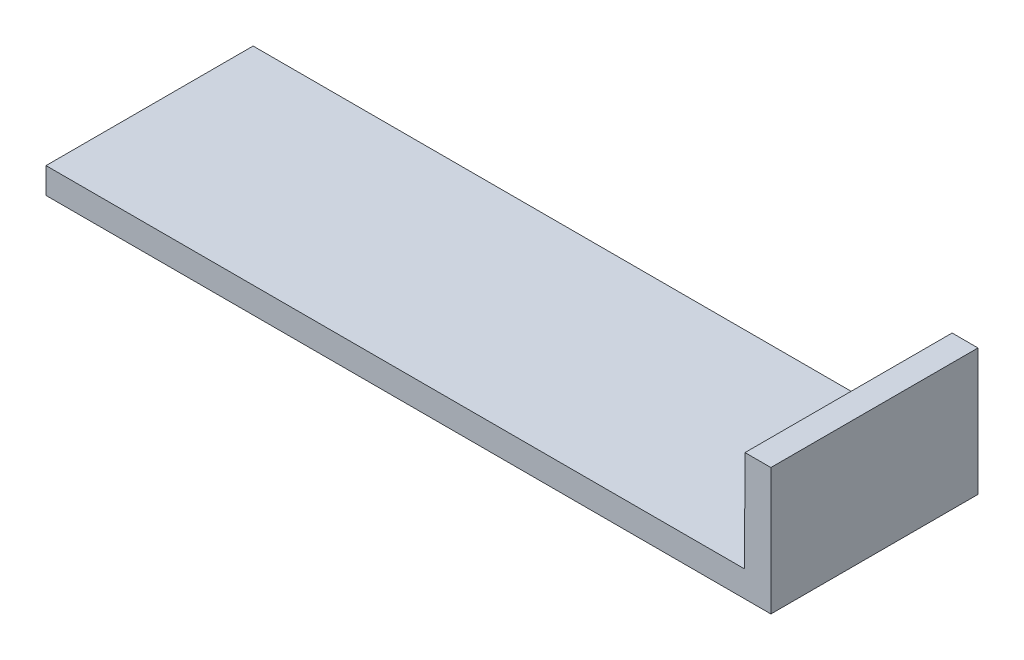
SolidWorks part; units mm, degrees
ref_plane "Front Plane" through (0, 0, 0) normal (0, 0, 1) x (1, 0, 0)
ref_plane "Top Plane" through (0, 0, 0) normal (0, 1, 0) x (1, 0, 0)
ref_plane "Right Plane" through (0, 0, 0) normal (1, 0, 0) x (0, 0, -1)
sketch "Sketch1" plane through (0, 0, 0) normal (0, 0, 1) x (1, 0, 0)
  line L0 (0, 0) -> (-88.9, 0)
  line L2 (-88.9, 0) -> (-88.9, 3.175)
  line L3 (-88.9, 3.175) -> (-3.2385, 3.175)
  line L4 (-3.2385, 3.175) -> (-3.175, 15.5575)
  line L5 (-3.175, 15.5575) -> (0, 15.5575)
  line L6 (0, 15.5575) -> (0, 0)
  dimension "D1" = 3.175
  dimension "D2" = 3.175
  dimension "D3" = 88.9
  dimension "D4" = 85.6615
  dimension "D5" = 15.5575
  dimension "D6" = 0
other "AlignGroup1"
other "AlignGroup2"
extrude "Boss-Extrude1" add sketch "Sketch1" along normal blind 25.4
